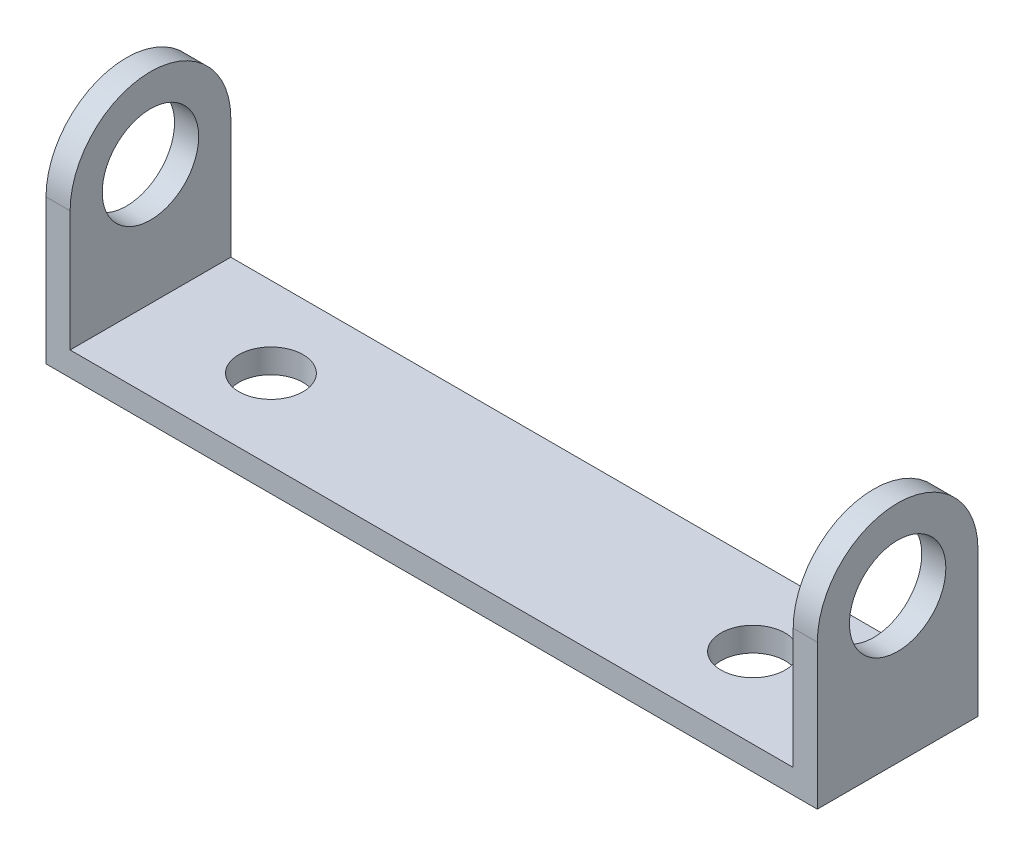
SolidWorks part; units mm, degrees
material "Plain Carbon Steel"
ref_plane "Front Plane" through (0, 0, 0) normal (0, 0, 1) x (1, 0, 0)
ref_plane "Top Plane" through (0, 0, 0) normal (0, 1, 0) x (1, 0, 0)
ref_plane "Right Plane" through (0, 0, 0) normal (1, 0, 0) x (0, 0, -1)
sketch "Sketch1" plane through (0, 0, 0) normal (0, 0, 1) x (1, 0, 0)
  line L0 (-22.5, 7) -> (-22.5, -5.5)
  line L1 (-24, -7) -> (24, -7)
  line L2 (-24, -7) -> (-24, 7)
  line L3 (-24, 7) -> (24, 7) construction
  line L4 (24, -7) -> (24, 7)
  line L5 (-24, -7) -> (24, 7) construction
  line L6 (-24, 7) -> (24, -7) construction
  line L7 (-22.5, -5.5) -> (22.5, -5.5)
  line L8 (22.5, -5.5) -> (22.5, 7)
  line L9 (24, 7) -> (22.5, 7)
  line L10 (-22.5, 7) -> (-24, 7)
  dimension "D1" = 48
  dimension "D2" = 14
  dimension "D3" = 1.5
  dimension "D4" = 1.5
  dimension "D5" = 1.5
extrude "Boss-Extrude1" add sketch "Sketch1" along normal blind 10
sketch "Sketch2" plane through (24, 0, 0) normal (1, 0, 0) x (0, 0, -1)
  line L0 (0, -7) -> (0, 7) construction
  line L1 (-10, -7) -> (-10, 7) construction
  line L2 (-10, 7) -> (0, 7) construction
  line L3 (-10, 2) -> (0, 2) construction
  line L4 (-10, 2) -> (-10, 7)
  line L5 (-10, 7) -> (0, 7)
  line L6 (0, 7) -> (0, 2)
  arc A0 (0, 2) -> (-10, 2) centre (-5, 2) ccw
  circle A1 centre (-5, 2) radius 3
  line M2 (0, -7) -> (0, 7)
  line M3 (0, 7) -> (-10, 7)
  line M4 (-10, 7) -> (-10, -7)
  dimension "D1" = 6
extrude "Cut-Extrude1" cut sketch "Sketch2" against normal up to surface (48 mm away) contours A0 L5 M4 | A0 M2 M3 | A1 L3 | L3 A1 up to face at (-24, 0, 5)
sketch "Sketch3" plane through (0, -5.5, 0) normal (0, 1, 0) x (1, 0, 0)
  line L0 (-22.5, 0) -> (22.5, -10) construction
  line L1 (22.5, 0) -> (-22.5, 0) construction
  line L2 (-22.5, -10) -> (-22.5, 0) construction
  line L3 (22.5, -10) -> (-22.5, -10) construction
  line L4 (0, -5) -> (22.5, -5) construction
  line L5 (22.5, -10) -> (22.5, 0) construction
  line L6 (0, -5) -> (-22.5, -5) construction
  circle A0 centre (15, -5) radius 2
  circle A1 centre (-15, -5) radius 2
  dimension "D1" = 4
  dimension "D2" = 4
  dimension "D3" = 15
  dimension "D4" = 15
extrude "Cut-Extrude2" cut sketch "Sketch3" against normal blind 10
